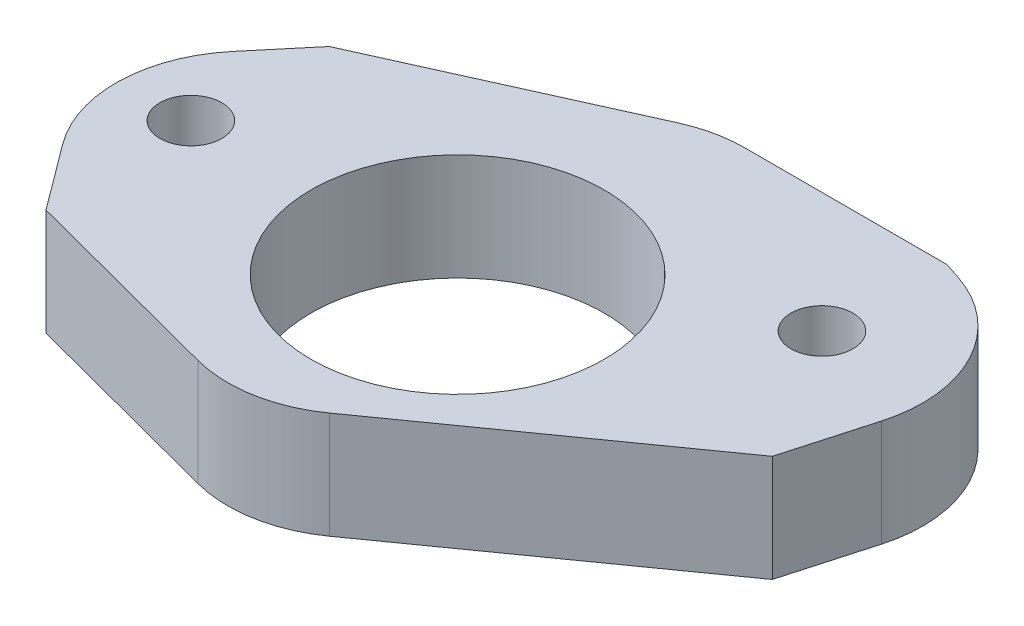
SolidWorks part; units mm, degrees
material "Rubber"
ref_plane "Front Plane" through (0, 0, 0) normal (0, 0, 1) x (1, 0, 0)
ref_plane "Top Plane" through (0, 0, 0) normal (0, 1, 0) x (1, 0, 0)
ref_plane "Right Plane" through (0, 0, 0) normal (1, 0, 0) x (0, 0, -1)
sketch "Sketch1" plane through (0, 0, 0) normal (0, 1, 0) x (1, 0, 0)
  line L0 (0, 0) -> (-10, 0) construction
  line L1 (0, 0) -> (8.6603, 5) construction
  line L2 (-9.8118, -5.6197) -> (0.1882, -8.25)
  line L3 (0.1882, -8.25) -> (11.7997, 0)
  line L4 (-9.8118, 5) -> (0.1882, 9.5)
  line L5 (0.1882, 9.5) -> (8.8485, 9.5)
  line L6 (8.8485, 9.5) -> (14, 7.8)
  line L7 (14, 7.8) -> (11.7997, 0)
  line L8 (-9.8118, 5) -> (-14, 0)
  line L9 (-14, 0) -> (-9.8118, -5.6197)
  circle A0 centre (0, 0) radius 5.5
  circle A1 centre (-10, 0) radius 1.1621
  circle A2 centre (8.6603, 5) radius 1.1621
  dimension "D1" = 11
  dimension "D2" = 10
  dimension "D4" = 150
  dimension "D5" = 14
  dimension "D6" = 14
  dimension "D7" = 7.8
  dimension "D8" = 9.5
  dimension "D3" = 2
extrude "Boss-Extrude1" add sketch "Sketch1" along normal blind 4
fillet "Fillet1" radius 5 4 edges at (0.1882, 2, -9.5) (0.1882, 2, 8.25) (14, 2, -7.8) (-14, 2, 0)
